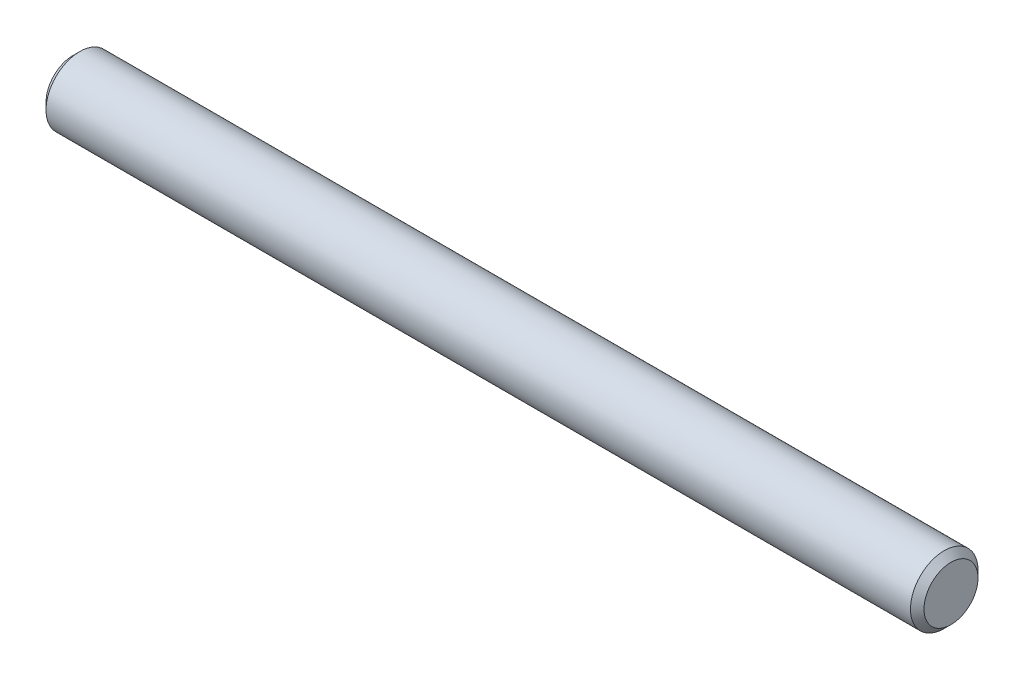
SolidWorks part; units mm, degrees
ref_plane "Front" through (0, 0, 0) normal (0, 0, 1) x (1, 0, 0)
ref_plane "Top" through (0, 0, 0) normal (0, 1, 0) x (1, 0, 0)
ref_plane "Right" through (0, 0, 0) normal (1, 0, 0) x (0, 0, -1)
sketch "Sketch1" plane through (0, 0, 0) normal (0, 0, 1) x (1, 0, 0)
  line L0 (-20.6375, 0) -> (20.6375, 0) construction
  line L1 (20.6375, 1.5875) -> (20.6375, -1.5875) construction
  line L2 (-20.6375, 1.5875) -> (-20.6375, -1.5875) construction
  dimension "Length" = 41.275
  dimension "Diameter" = 3.175
sketch "Sketch2" plane through (0, 0, 0) normal (1, 0, 0) x (0, 0, -1)
  circle A0 centre (0, 0) radius 1.5875
extrude "Extrude1" add sketch "Sketch2" against normal up to vertex (20.6375 mm away) and the other way up to vertex (20.6375 mm away) up to point (-20.6375, 1.5875, 0) other way up to point (20.6375, 1.5875, 0)
chamfer "Chamfer1" distance 0.3175 angle 45 2 edges at (20.6375, 0, -1.5875) (-20.6375, 0, -1.5875)
equation "\"D1@Chamfer1\" = \"Diameter@Sketch1\"*.1"
